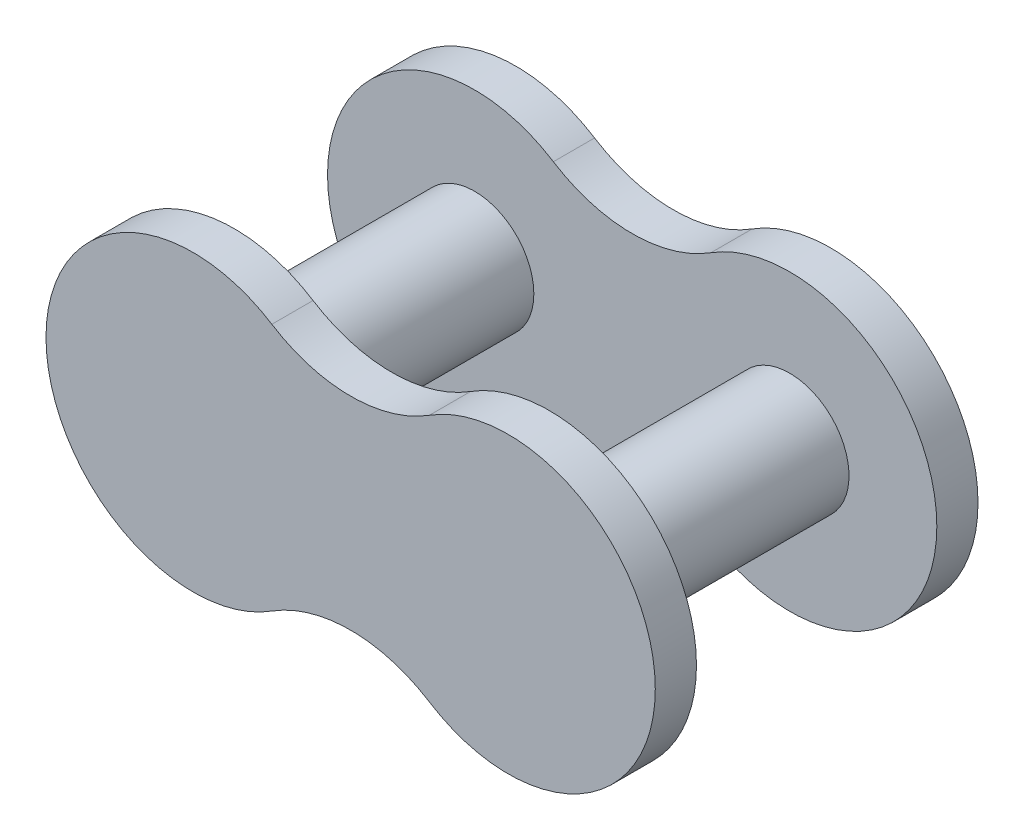
SolidWorks part; units mm, degrees
ref_plane "Front Plane" through (0, 0, 0) normal (0, 0, 1) x (1, 0, 0)
ref_plane "Top Plane" through (0, 0, 0) normal (0, 1, 0) x (1, 0, 0)
ref_plane "Right Plane" through (0, 0, 0) normal (1, 0, 0) x (0, 0, -1)
sketch "Sketch1" plane through (0, 0, 0) normal (0, 0, 1) x (1, 0, 0)
  line L0 (0, 0) -> (0, 3.0187) construction
  line L1 (0, 0) -> (2.5976, 0) construction
  circle A0 centre (-4.7625, 0) radius 1.7907
  circle A1 centre (4.7625, 0) radius 1.7907
  dimension "D1" = 3.5814
  dimension "D2" = 9.525
extrude "Boss-Extrude1" add sketch "Sketch1" along normal mid plane 7.2644
sketch "Sketch3" plane through (0, 0, 3.6322) normal (0, 0, 1) x (1, 0, 0)
  line L0 (0, 0) -> (0, 2.7323) construction
  line L1 (0, 0) -> (1.8415, 0) construction
  arc A0 (-2.3813, 3.7534) -> (-2.3813, -3.7534) centre (-4.7625, 0) ccw
  circle A1 centre (-4.7625, 0) radius 1.7907 construction
  arc A2 (2.3813, 3.7534) -> (2.3813, -3.7534) centre (4.7625, 0) cw
  arc A3 (-2.3813, 3.7534) -> (2.3813, 3.7534) centre (0, 7.5067) ccw
  arc A4 (-2.3813, -3.7534) -> (2.3813, -3.7534) centre (0, -7.5067) cw
  dimension "D1" = 8.89
  dimension "D2" = 4.445
extrude "Boss-Extrude2" add sketch "Sketch3" along normal blind 1.2446
mirror "Mirror1" about plane through (0, 0, 0) normal (0, 0, 1) of "Boss-Extrude2"
